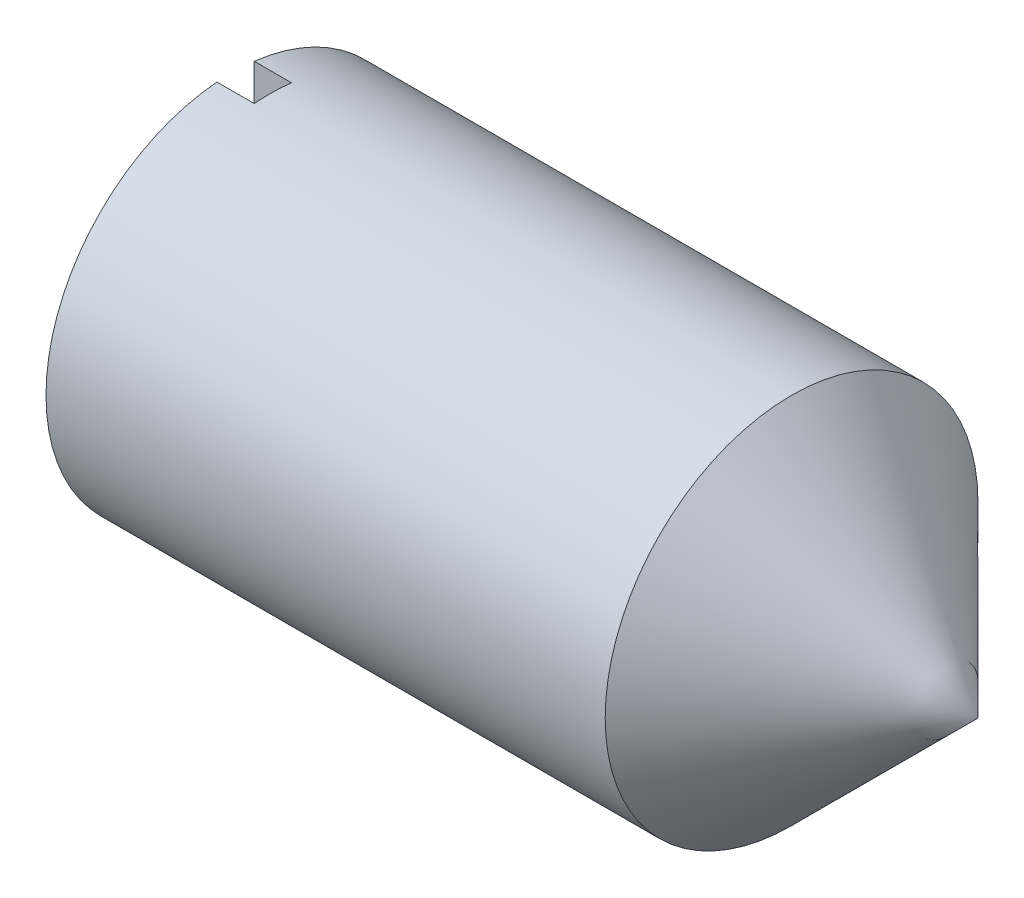
SolidWorks part; units mm, degrees
ref_plane "Front Plane" through (0, 0, 0) normal (0, 0, 1) x (1, 0, 0)
ref_plane "Top Plane" through (0, 0, 0) normal (0, 1, 0) x (1, 0, 0)
ref_plane "Right Plane" through (0, 0, 0) normal (1, 0, 0) x (0, 0, -1)
sketch "Sketch1" plane through (0, 0, 0) normal (0, 1, 0) x (1, 0, 0)
  line L0 (7.62, -5.08) -> (10.16, -2.54)
  line L1 (0, 0) -> (7.62, 0)
  line L2 (0, 0) -> (0, -5.08)
  line L3 (0, -5.08) -> (7.62, -5.08)
  line L4 (7.62, 0) -> (7.62, -5.08)
  line L5 (10.16, -2.54) -> (7.62, 0)
  line L6 (10.16, -2.54) -> (0, -2.54)
  dimension "D1" = 5.08
  dimension "D2" = 7.62
  dimension "D3" = 2.54
revolve "Revolve1" add sketch "Sketch1" angle 360 about L6
sketch "Sketch2" plane through (0, 0, 0) normal (-1, 0, 0) x (0, 0, 1)
  line L1 (2.2425, 2.6965) -> (2.7505, 2.6965)
  line L2 (2.2425, 2.6965) -> (2.2425, -2.7342)
  line L3 (2.2425, -2.7342) -> (2.7505, -2.7342)
  line L4 (2.7505, 2.6965) -> (2.7505, -2.7342)
  point P4 (2.54, 0)
  dimension "D1" = 0.508
  dimension "D2" = 0.2105
extrude "Cut-Extrude1" cut sketch "Sketch2" against normal blind 0.508
